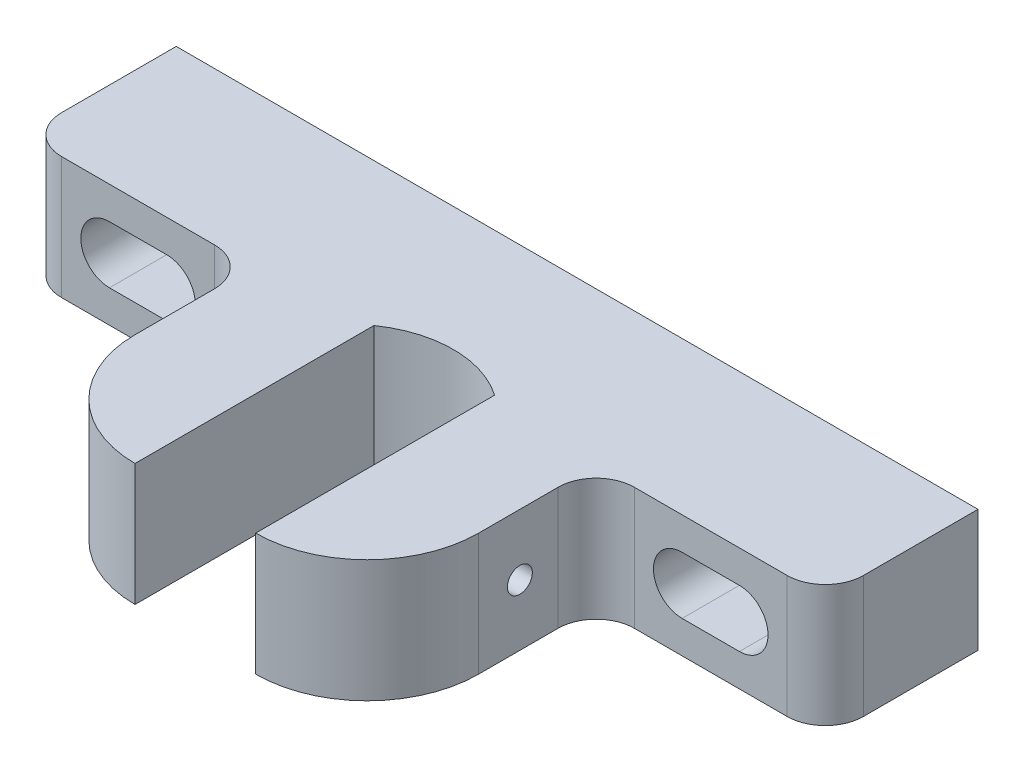
SolidWorks part; units mm, degrees
material "6061 Alloy"
ref_plane "Front Plane" through (0, 0, 0) normal (0, 0, 1) x (1, 0, 0)
ref_plane "Top Plane" through (0, 0, 0) normal (0, 1, 0) x (1, 0, 0)
ref_plane "Right Plane" through (0, 0, 0) normal (1, 0, 0) x (0, 0, -1)
sketch "Sketch1" plane through (0, 0, 0) normal (0, 0, 1) x (1, 0, 0)
  line L1 (-66.675, 24.2888) -> (66.675, 24.2888)
  line L2 (-66.675, 24.2888) -> (-66.675, 3.9688)
  line L3 (-66.675, 3.9688) -> (66.675, 3.9688)
  line L4 (66.675, 24.2888) -> (66.675, 3.9688)
  line L6 (-47.625, 14.1288) -> (-66.675, 14.1288) construction
  line L8 (0, 24.2888) -> (0, 0) construction
  circle A0 centre (-47.625, 14.1288) radius 4.7625 construction
  circle A2 centre (47.625, 14.1288) radius 4.7625 construction
  dimension "D3" = 9.525
  dimension "D1" = 20.32
  dimension "D2" = 133.35
  dimension "D4" = 3.9688
  dimension "D5" = 95.25
extrude "Extrude1" add sketch "Sketch1" along normal blind 63.5
sketch "Sketch2" plane through (0, 3.9688, 0) normal (0, -1, 0) x (1, 0, 0)
  line L0 (-10.033, 23.7616) -> (-10.033, 63.5)
  line L1 (-66.675, 63.5) -> (66.675, 63.5) construction
  line L2 (0, 1.9106) -> (0, 81.6959) construction
  line L3 (-10.033, 63.5) -> (-66.675, 25.4) construction
  line L4 (-66.675, 81.6959) -> (66.675, 81.6959)
  line L5 (66.675, 81.6959) -> (66.675, 63.5)
  line L6 (-66.675, 0) -> (66.675, 0) construction
  line L7 (28.575, 44.958) -> (28.575, 31.75)
  line L8 (-66.675, 63.5) -> (-66.675, 25.4)
  line L9 (-66.675, 25.4) -> (-34.925, 25.4)
  line L10 (-28.575, 44.958) -> (-28.575, 31.75)
  line L11 (66.675, 25.4) -> (34.925, 25.4)
  line L12 (66.675, 63.5) -> (66.675, 25.4)
  line L13 (10.033, 23.7616) -> (10.033, 63.5)
  line L14 (-66.675, 81.6959) -> (-66.675, 63.5)
  arc A0 (-34.925, 25.4) -> (-28.575, 31.75) centre (-34.925, 31.75) ccw
  arc A1 (10.033, 23.7616) -> (-10.033, 23.7616) centre (0, 38.1) cw
  arc A2 (-10.033, 63.5) -> (-28.575, 44.958) centre (-10.033, 44.958) ccw
  arc A3 (10.033, 63.5) -> (28.575, 44.958) centre (10.033, 44.958) cw
  arc A5 (34.925, 25.4) -> (28.575, 31.75) centre (34.925, 31.75) cw
  dimension "D1" = 38.1
  dimension "D3" = 6.35
  dimension "D4" = 17.5
  dimension "D2" = 25.4
extrude "Cut-Extrude1" cut sketch "Sketch2" against normal through all
fillet "Fillet1" radius 6.35 2 edges at (-66.675, 14.1288, 25.4) (66.675, 14.1288, 25.4)
sketch "Sketch3" plane through (0, 0, 0) normal (0, 0, -1) x (-1, 0, 0)
  line L0 (0, 24.2888) -> (0, 0) construction
  line L1 (-52.3875, 18.8913) -> (-42.8625, 18.8913)
  line L2 (-52.3875, 18.8913) -> (-52.3875, 9.3663) construction
  line L3 (-52.3875, 9.3663) -> (-42.8625, 9.3663)
  line L4 (-42.8625, 18.8913) -> (-42.8625, 9.3663) construction
  line L5 (0, 24.2888) -> (0, 0) construction
  line L6 (52.3875, 9.3663) -> (42.8625, 9.3663)
  line L7 (52.3875, 18.8913) -> (42.8625, 18.8913)
  circle A2 centre (-47.625, 14.1288) radius 4.7625 construction
  arc A3 (-42.8625, 18.8913) -> (-42.8625, 9.3663) centre (-42.8625, 14.1288) cw
  arc A4 (-52.3875, 9.3663) -> (-52.3875, 18.8913) centre (-52.3875, 14.1288) cw
  arc A5 (52.3875, 9.3663) -> (52.3875, 18.8913) centre (52.3875, 14.1288) ccw
  arc A6 (42.8625, 18.8913) -> (42.8625, 9.3663) centre (42.8625, 14.1288) ccw
extrude "Cut-Extrude2" cut sketch "Sketch3" against normal through all
sketch "Sketch6" plane through (0, 0, 0) normal (1, 0, 0) x (0, 0, -1)
  line L0 (0, 14.1288) -> (-38.1, 14.1288) construction
  line L1 (0, 3.9688) -> (0, 24.2888) construction
  circle A0 centre (-38.1, 14.1288) radius 2.0764
  dimension "D1" = 4.1529
  dimension "D2" = 38.1
extrude "Cut-Extrude5" cut sketch "Sketch6" along normal through all
